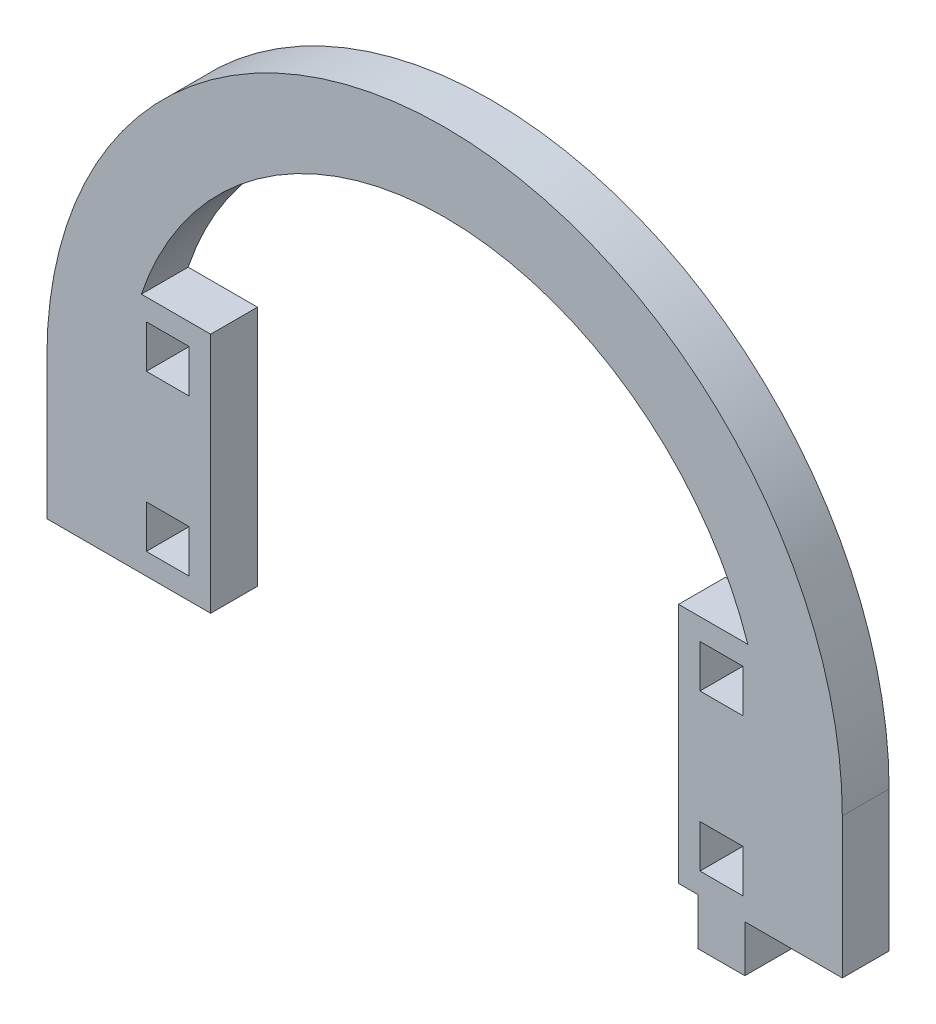
SolidWorks part; units mm, degrees
ref_plane "Front Plane" through (0, 0, 0) normal (0, 0, 1) x (1, 0, 0)
ref_plane "Top Plane" through (0, 0, 0) normal (0, 1, 0) x (1, 0, 0)
ref_plane "Right Plane" through (0, 0, 0) normal (1, 0, 0) x (0, 0, -1)
sketch "Model" plane through (0, 0, 0) normal (0, 0, 1) x (1, 0, 0)
  line L0 (3030.3705, 1416.7889) -> (3030.3705, 1398.7889)
  line L1 (3132.3705, 1416.7889) -> (3132.3705, 1398.7889)
  line L2 (3040.3705, 1398.7889) -> (3030.3705, 1398.7889)
  line L3 (3119.6205, 1407.0389) -> (3114.1205, 1407.0389)
  line L4 (3114.1205, 1407.0389) -> (3114.1205, 1401.5389)
  line L5 (3114.1205, 1401.5389) -> (3119.6205, 1401.5389)
  line L6 (3119.6205, 1401.5389) -> (3119.6205, 1407.0389)
  line L7 (3111.3705, 1398.7889) -> (3113.8705, 1398.7889)
  line L8 (3113.8705, 1398.7889) -> (3113.8705, 1392.7889)
  line L9 (3113.8705, 1392.7889) -> (3119.8705, 1392.7889)
  line L10 (3119.8705, 1392.7889) -> (3119.8705, 1398.7889)
  line L11 (3119.6205, 1427.0389) -> (3114.1205, 1427.0389)
  line L12 (3114.1205, 1427.0389) -> (3114.1205, 1421.5389)
  line L13 (3114.1205, 1421.5389) -> (3119.6205, 1421.5389)
  line L14 (3119.6205, 1421.5389) -> (3119.6205, 1427.0389)
  line L15 (3120.2549, 1429.7889) -> (3111.3705, 1429.7889)
  line L16 (3048.6205, 1407.0389) -> (3043.1205, 1407.0389)
  line L17 (3043.1205, 1407.0389) -> (3043.1205, 1401.5389)
  line L18 (3043.1205, 1401.5389) -> (3048.6205, 1401.5389)
  line L19 (3048.6205, 1401.5389) -> (3048.6205, 1407.0389)
  line L20 (3040.3705, 1398.7889) -> (3051.3705, 1398.7889)
  line L21 (3048.6205, 1427.0389) -> (3043.1205, 1427.0389)
  line L22 (3043.1205, 1427.0389) -> (3043.1205, 1421.5389)
  line L23 (3043.1205, 1421.5389) -> (3048.6205, 1421.5389)
  line L24 (3048.6205, 1421.5389) -> (3048.6205, 1427.0389)
  line L25 (3051.3705, 1429.7889) -> (3042.486, 1429.7889)
  line L26 (3051.3705, 1429.7889) -> (3051.3705, 1398.7889)
  line L27 (3111.3705, 1429.7889) -> (3111.3705, 1398.7889)
  line L28 (3119.8705, 1398.7889) -> (3132.3705, 1398.7889)
  arc A0 (3132.3705, 1416.7889) -> (3030.3705, 1416.7889) centre (3081.3705, 1416.7889) ccw
  arc A1 (3120.2549, 1429.7889) -> (3042.486, 1429.7889) centre (3081.3705, 1416.7889) ccw
extrude "Boss-Extrude1" add sketch "Model" along normal blind 6 contours L18 L19 L16 L17 | L13 L14 L11 L12 | L5 L6 L3 L4 | L0 L2 L20 L26 L25 A1 L15 L27 L7 L8 L9 L10 L28 L1 A0 | L22 L23 L24 L21
